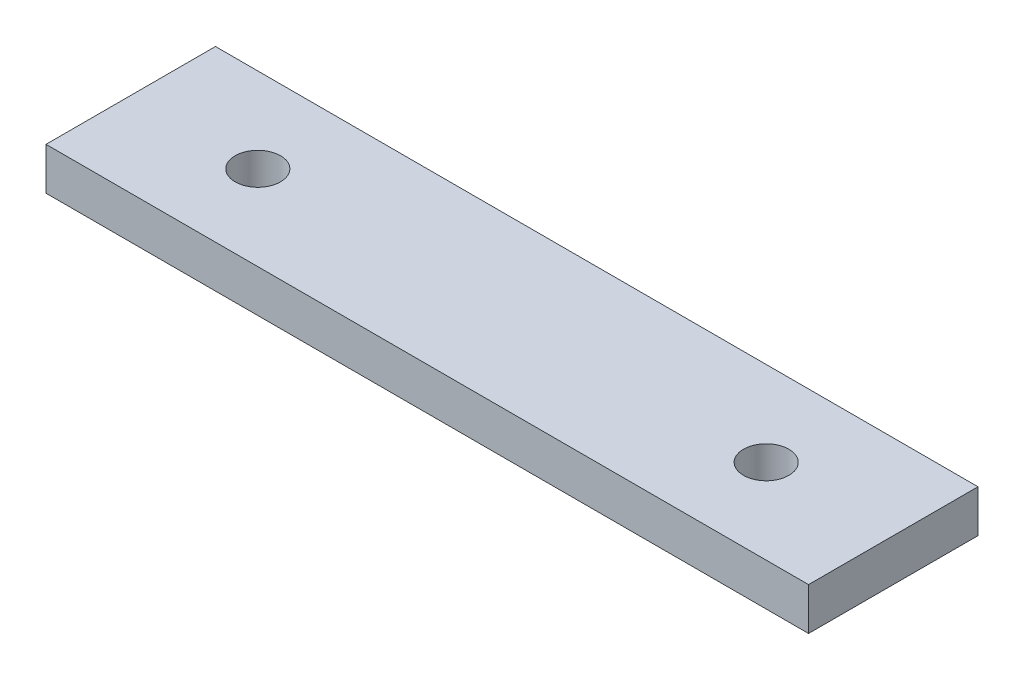
SolidWorks part; units mm, degrees
ref_plane "Front Plane" through (0, 0, 0) normal (0, 0, 1) x (1, 0, 0)
ref_plane "Top Plane" through (0, 0, 0) normal (0, 1, 0) x (1, 0, 0)
ref_plane "Right Plane" through (0, 0, 0) normal (1, 0, 0) x (0, 0, -1)
sketch "Sketch1" plane through (0, 0, 0) normal (0, 1, 0) x (1, 0, 0)
  line L0 (-38.1, 0) -> (38.1, 0) construction
  line L1 (-57.15, 12.7) -> (57.15, 12.7)
  line L2 (-57.15, 12.7) -> (-57.15, -12.7)
  line L3 (-57.15, -12.7) -> (57.15, -12.7)
  line L4 (57.15, 12.7) -> (57.15, -12.7)
  line L5 (-57.15, 12.7) -> (57.15, -12.7) construction
  line L6 (-57.15, -12.7) -> (57.15, 12.7) construction
  circle A0 centre (-38.1, 0) radius 3.4
  circle A1 centre (38.1, 0) radius 3.4
  point P0 (0, 0)
  point P12 (0, 0)
  point P13 (0, 0)
  point P14 (0, 0)
  dimension "D4" = 6.8
  dimension "D5" = 6.8
  dimension "D1" = 114.3
  dimension "D2" = 25.4
  dimension "D3" = 76.2
extrude "Boss-Extrude1" add sketch "Sketch1" along normal blind 6.35
